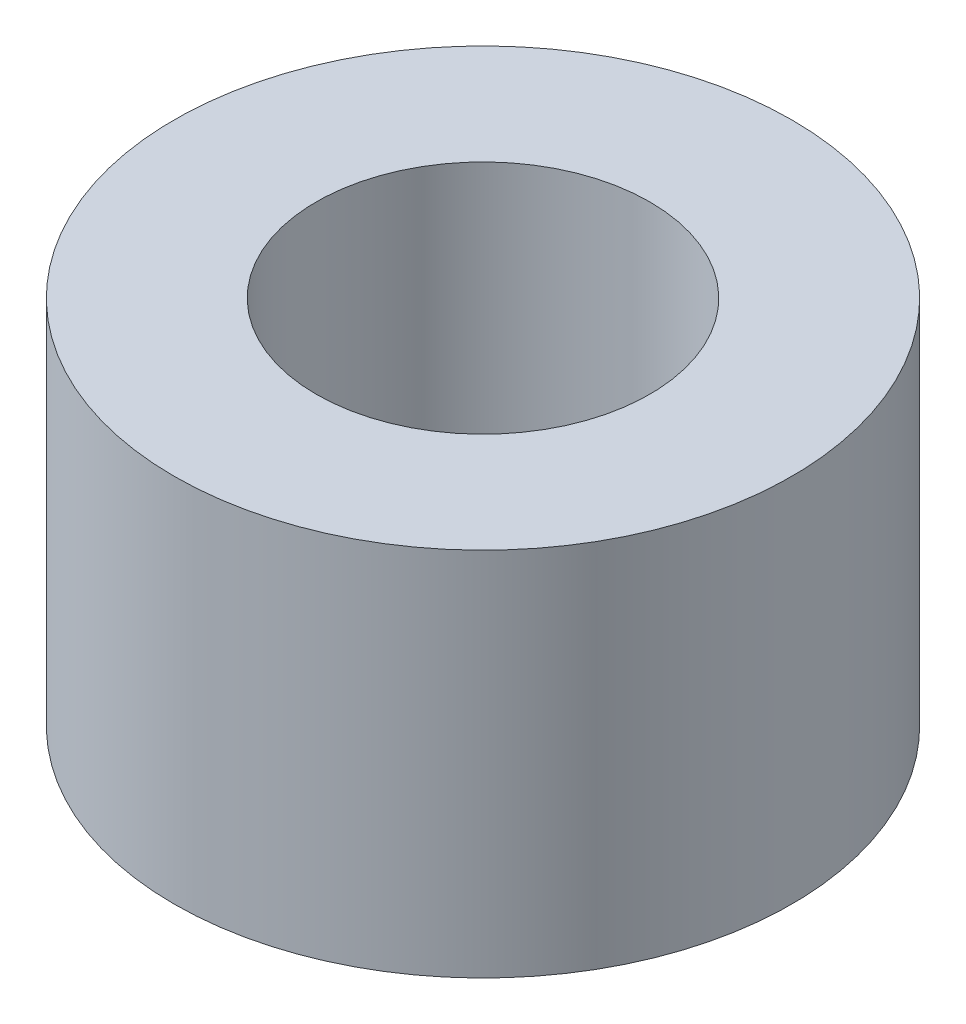
SolidWorks part; units mm, degrees
ref_plane "Front Plane" through (0, 0, 0) normal (0, 0, 1) x (1, 0, 0)
ref_plane "Top Plane" through (0, 0, 0) normal (0, 1, 0) x (1, 0, 0)
ref_plane "Right Plane" through (0, 0, 0) normal (1, 0, 0) x (0, 0, -1)
sketch "Sketch1" plane through (0, 0, 0) normal (0, 1, 0) x (1, 0, 0)
  circle A0 centre (0, 0) radius 2.7
  circle A1 centre (0, 0) radius 5
  dimension "D1" = 5.4
  dimension "D2" = 10
extrude "Boss-Extrude1" add sketch "Sketch1" along normal blind 6
